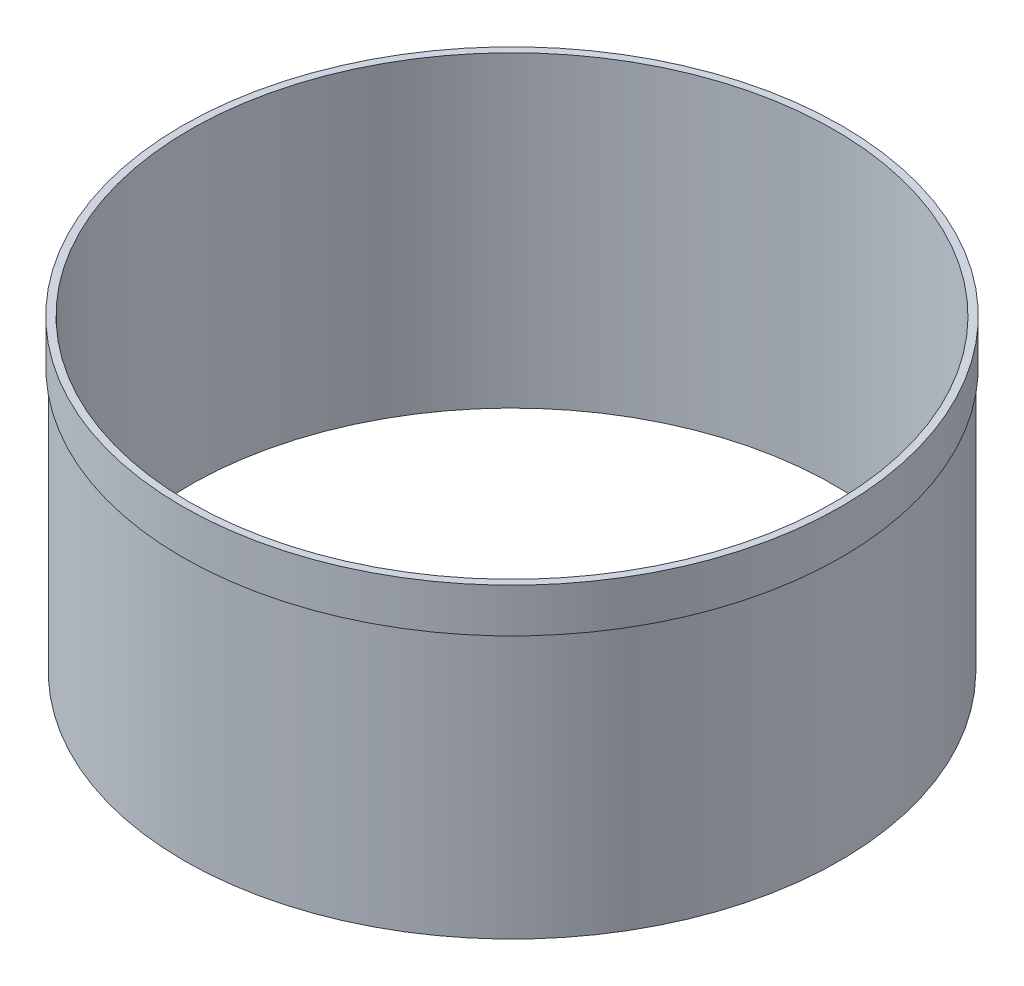
SolidWorks part; units mm, degrees
material "A-Glass Fiber"
ref_plane "Front Plane" through (0, 0, 0) normal (0, 0, 1) x (1, 0, 0)
ref_plane "Top Plane" through (0, 0, 0) normal (0, 1, 0) x (1, 0, 0)
ref_plane "Right Plane" through (0, 0, 0) normal (1, 0, 0) x (0, 0, -1)
sketch "Sketch1" plane through (0, 0, 0) normal (0, 1, 0) x (1, 0, 0)
  circle A0 centre (0, 0) radius 94.742
  circle A1 centre (0, 0) radius 93.1545
  dimension "D1" = 1.5875
  dimension "D2" = 189.484
extrude "Boss-Extrude1" add sketch "Sketch1" along normal blind 88.9
sketch "Sketch2" plane through (0, 88.9, 0) normal (0, 1, 0) x (1, 0, 0)
  circle A0 centre (0, 0) radius 94.742 construction
  circle A1 centre (0, 0) radius 94.742
  circle A2 centre (0, 0) radius 95.25
  dimension "D1" = 190.5
extrude "Boss-Extrude2" add sketch "Sketch2" against normal blind 12.7
